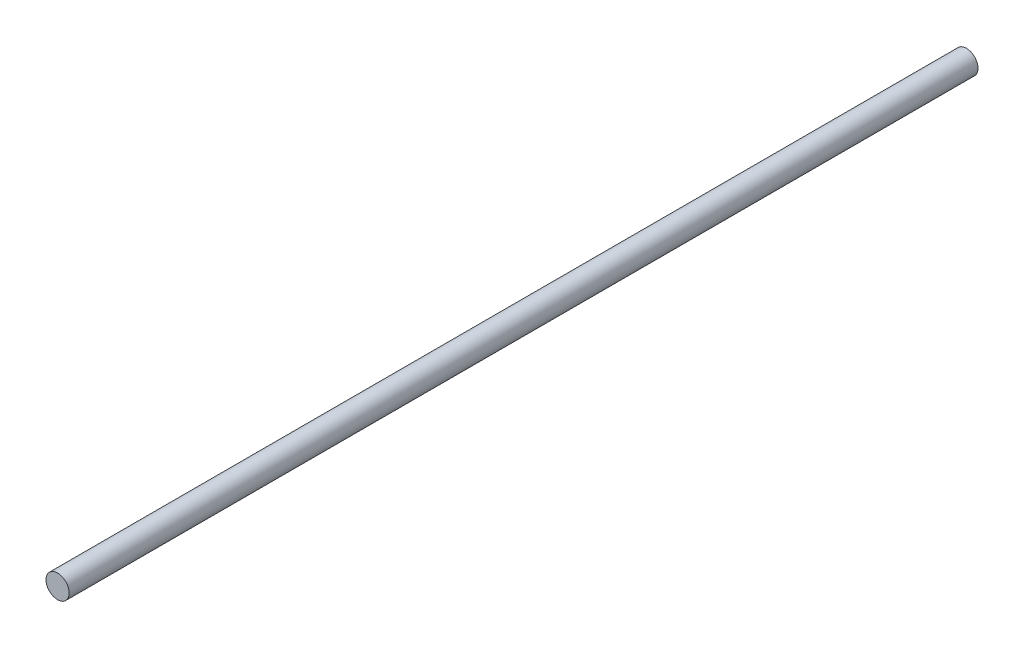
SolidWorks part; units mm, degrees
material "Teak"
ref_plane "Front Plane" through (0, 0, 0) normal (0, 0, 1) x (1, 0, 0)
ref_plane "Top Plane" through (0, 0, 0) normal (0, 1, 0) x (1, 0, 0)
ref_plane "Right Plane" through (0, 0, 0) normal (1, 0, 0) x (0, 0, -1)
sketch "Sketch1" plane through (0, 0, 0) normal (0, 0, 1) x (1, 0, 0)
  circle A0 centre (0, 0) radius 3.95
  dimension "D1" = 7.9
extrude "Boss-Extrude1" add sketch "Sketch1" along normal blind 310
